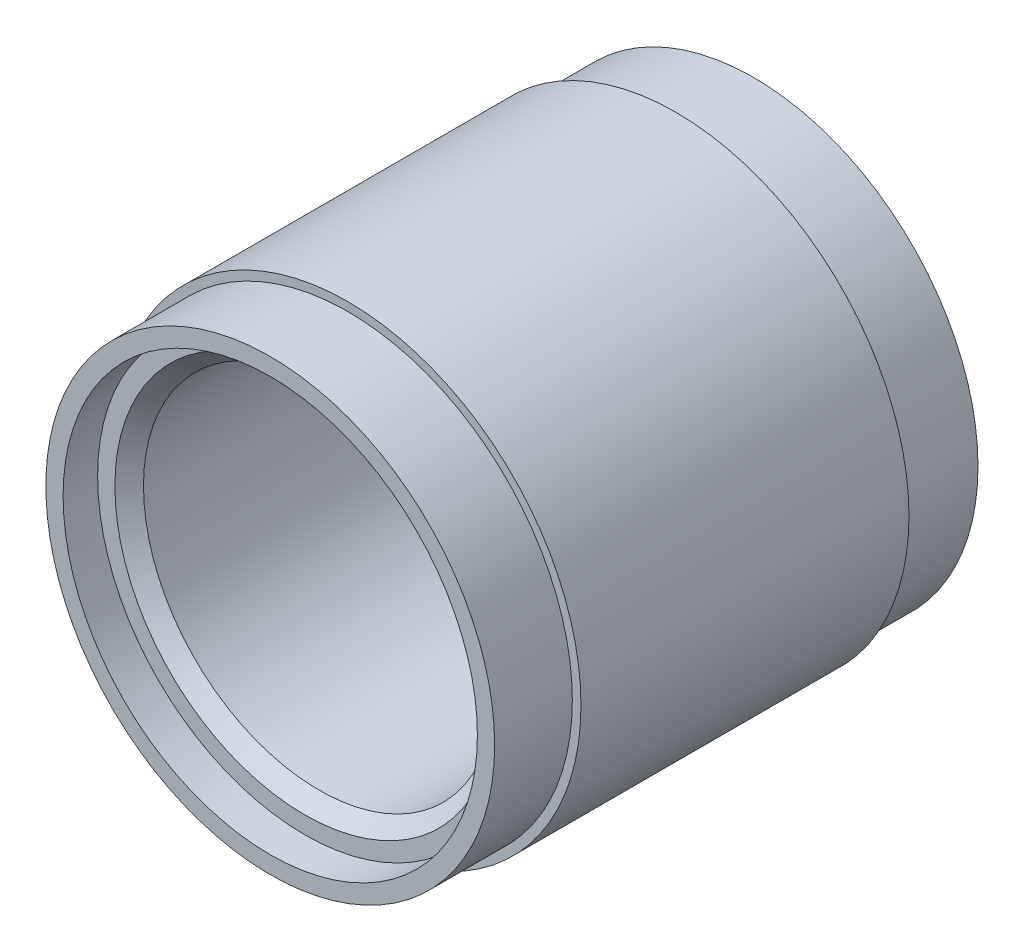
SolidWorks part; units mm, degrees
material "Сталь"
ref_plane "Спереди" through (0, 0, 0) normal (0, 0, 1) x (1, 0, 0)
ref_plane "Сверху" through (0, 0, 0) normal (0, 1, 0) x (1, 0, 0)
ref_plane "Справа" through (0, 0, 0) normal (1, 0, 0) x (0, 0, -1)
sketch "Эскиз2" plane through (0, 0, 0) normal (0, 0, 1) x (1, 0, 0)
  circle A0 centre (0, 0) radius 13
  dimension "D1" = 26
extrude "Бобышка-Вытянуть1" add sketch "Эскиз2" along normal blind 4.5
sketch "Эскиз3" plane through (0, 0, 4.5) normal (0, 0, 1) x (1, 0, 0)
  circle A0 centre (0, 0) radius 13.5
  dimension "D1" = 27
extrude "Бобышка-Вытянуть2" add sketch "Эскиз3" along normal blind 9.5
sketch "Эскиз4" plane through (0, 0, 0) normal (0, 0, -1) x (-1, 0, 0)
  circle A0 centre (0, 0) radius 12
  dimension "D1" = 24
extrude "Вырез-Вытянуть1" cut sketch "Эскиз4" against normal blind 2
mirror "Зеркальное отражение4" about plane through (0, 0, 14) normal (0, 0, 1) of bodies 107
sketch "Эскиз5" plane through (0, 0, 2) normal (0, 0, -1) x (-1, 0, 0)
  circle A0 centre (0, 0) radius 10.172
  dimension "D1" = 20.344
extrude "Вырез-Вытянуть2" cut sketch "Эскиз5" against normal through all
cosmetic thread "Условное изображение резьбы1" parameters "D2"=22
chamfer "Фаска1" distance 0.828 angle 45 2 edges at (10.172, 0, 26) (-10.172, 0, 2)
